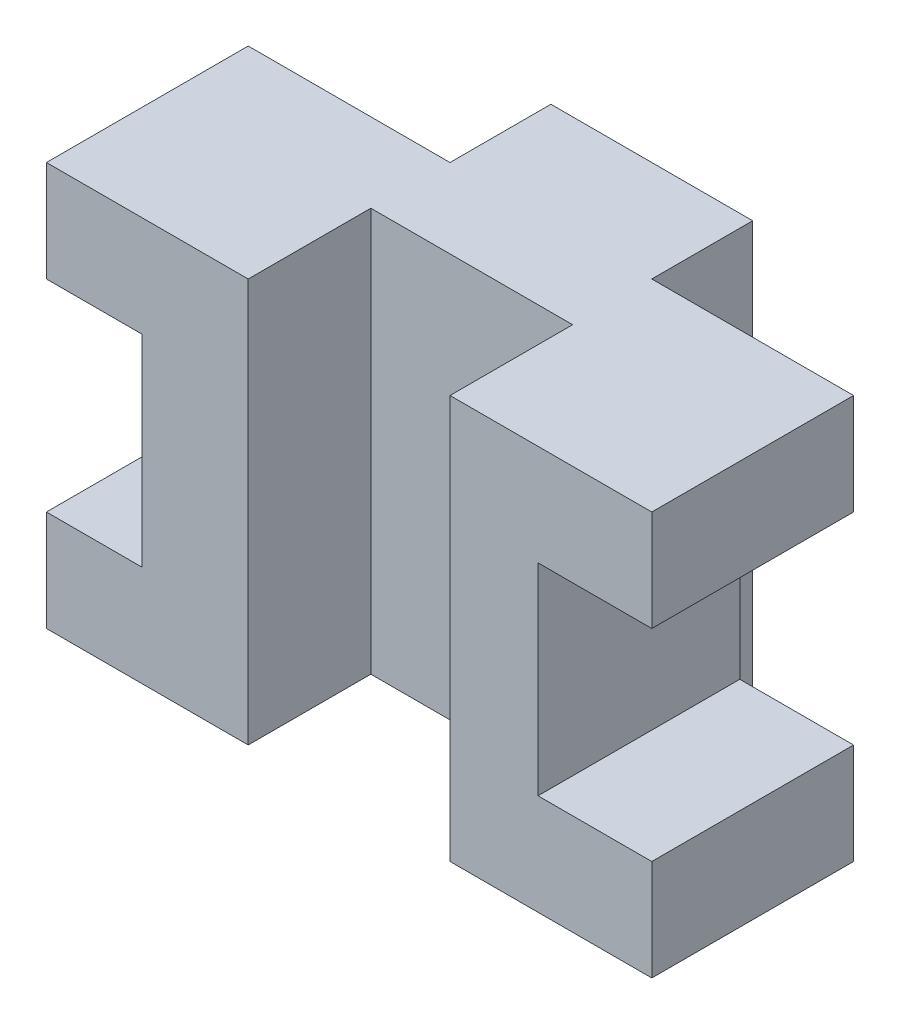
SolidWorks part; units mm, degrees
material "Cobre"
ref_plane "Alzado" through (0, 0, 0) normal (0, 0, 1) x (1, 0, 0)
ref_plane "Planta" through (0, 0, 0) normal (0, 1, 0) x (1, 0, 0)
ref_plane "Vista lateral" through (0, 0, 0) normal (1, 0, 0) x (0, 0, -1)
sketch "Croquis1" plane through (0, 0, 0) normal (0, 1, 0) x (1, 0, 0)
  line L1 (-30, 15) -> (30, 15)
  line L2 (-30, 15) -> (-30, -15)
  line L3 (-30, -15) -> (30, -15)
  line L4 (30, 15) -> (30, -15)
  line L5 (-30, 15) -> (30, -15) construction
  line L6 (-30, -15) -> (30, 15) construction
  point P0 (0, 0)
  dimension "D1" = 60
  dimension "D2" = 30
extrude "Saliente-Extruir2" add sketch "Croquis1" along normal blind 40
sketch "Croquis2" plane through (0, 40, 0) normal (0, 1, 0) x (1, 0, 0)
  line L0 (-30, -15) -> (30, -15) construction
  line L1 (-10, -15) -> (10, -15)
  line L2 (-10, -15) -> (-10, -2.8463)
  line L3 (-10, -2.8463) -> (10, -2.8463)
  line L4 (10, -15) -> (10, -2.8463)
  dimension "D1" = 20
  dimension "D2" = 20
extrude "Cortar-Extruir1" cut sketch "Croquis2" against normal through all
sketch "Croquis3" plane through (0, 40, 0) normal (0, 1, 0) x (1, 0, 0)
  line L1 (-30, 15) -> (-10, 15)
  line L2 (-30, 15) -> (-30, 5)
  line L3 (-30, 5) -> (-10, 5)
  line L4 (-10, 15) -> (-10, 5)
  dimension "D1" = 10
  dimension "D2" = 20
extrude "Cortar-Extruir2" cut sketch "Croquis3" against normal through all
sketch "Croquis4" plane through (0, 40, 0) normal (0, 1, 0) x (1, 0, 0)
  line L1 (30, 15) -> (10, 15)
  line L2 (30, 15) -> (30, 5)
  line L3 (30, 5) -> (10, 5)
  line L4 (10, 15) -> (10, 5)
  dimension "D1" = 10
  dimension "D2" = 20
extrude "Cortar-Extruir3" cut sketch "Croquis4" against normal through all
sketch "Croquis5" plane through (0, 0, 15) normal (0, 0, 1) x (1, 0, 0)
  line L0 (30, 40) -> (30, 0) construction
  line L1 (30, 30) -> (18.7234, 30)
  line L2 (30, 30) -> (30, 10)
  line L3 (30, 10) -> (18.7234, 10)
  line L4 (18.7234, 30) -> (18.7234, 10)
  dimension "D1" = 10
  dimension "D2" = 10
extrude "Cortar-Extruir4" cut sketch "Croquis5" against normal blind 40
sketch "Croquis6" plane through (0, 0, 15) normal (0, 0, 1) x (1, 0, 0)
  line L0 (-30, 40) -> (-30, 0) construction
  line L1 (-30, 30) -> (-20.5115, 30)
  line L2 (-30, 30) -> (-30, 10)
  line L3 (-30, 10) -> (-20.5115, 10)
  line L4 (-20.5115, 30) -> (-20.5115, 10)
  dimension "D1" = 10
  dimension "D2" = 10
extrude "Cortar-Extruir5" cut sketch "Croquis6" against normal blind 40
